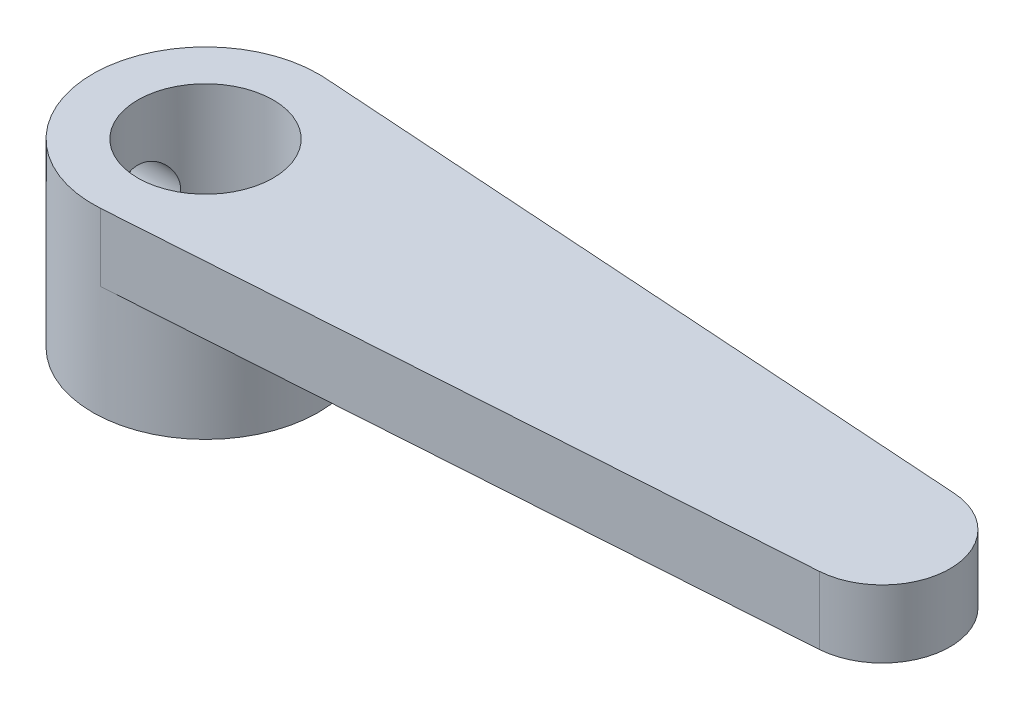
SolidWorks part; units mm, degrees
ref_plane "前基準面" through (0, 0, 0) normal (0, 0, 1) x (1, 0, 0)
ref_plane "上基準面" through (0, 0, 0) normal (0, 1, 0) x (1, 0, 0)
ref_plane "右基準面" through (0, 0, 0) normal (1, 0, 0) x (0, 0, -1)
sketch "草圖1" plane through (0, 0, 0) normal (0, 1, 0) x (1, 0, 0)
  line L0 (0.3333, 4.9889) -> (30.2, 2.9933)
  line L1 (0.3333, -4.9889) -> (30.2, -2.9933)
  circle A0 centre (0, 0) radius 3
  arc A1 (0.3333, 4.9889) -> (0.3333, -4.9889) centre (0, 0) ccw
  arc A2 (30.2, 2.9933) -> (30.2, -2.9933) centre (30, 0) cw
  point P8 (0, 0)
  point P9 (0, 0)
  dimension "D1" = 6
  dimension "D2" = 5
  dimension "D3" = 3
  dimension "D4" = 30
extrude "填料-伸長1" add sketch "草圖1" along normal blind 3
sketch "草圖2" plane through (0, 0, 0) normal (0, -1, 0) x (1, 0, 0)
  circle A0 centre (0, 0) radius 3 construction
  circle A1 centre (0, 0) radius 3
  circle A2 centre (0, 0) radius 5
  dimension "D1" = 10
extrude "填料-伸長2" add sketch "草圖2" along normal blind 5
sketch "草圖3" plane through (0, 0, 0) normal (1, 0, 0) x (0, 0, -1)
  line L0 (-5, -5) -> (5, -5) construction
  circle A0 centre (0, -1) radius 1.5
  point P4 (0, 0)
  dimension "D1" = 3
  dimension "D2" = 4
extrude "除料-伸長1" cut sketch "草圖3" against normal through all
